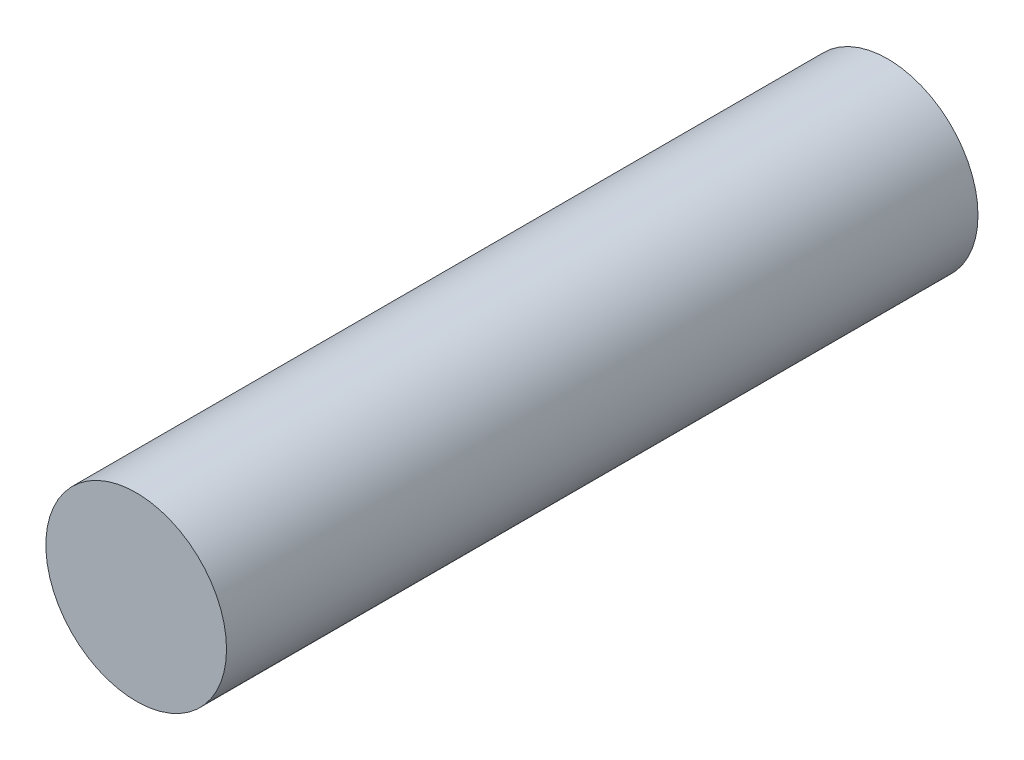
SolidWorks part; units mm, degrees
ref_plane "Front Plane" through (0, 0, 0) normal (0, 0, 1) x (1, 0, 0)
ref_plane "Top Plane" through (0, 0, 0) normal (0, 1, 0) x (1, 0, 0)
ref_plane "Right Plane" through (0, 0, 0) normal (1, 0, 0) x (0, 0, -1)
sketch "Sketch1" plane through (0, 0, 0) normal (0, 0, 1) x (1, 0, 0)
  circle A0 centre (0, 0) radius 17.526
extrude "Boss-Extrude1" add sketch "Sketch1" along normal blind 145.78
